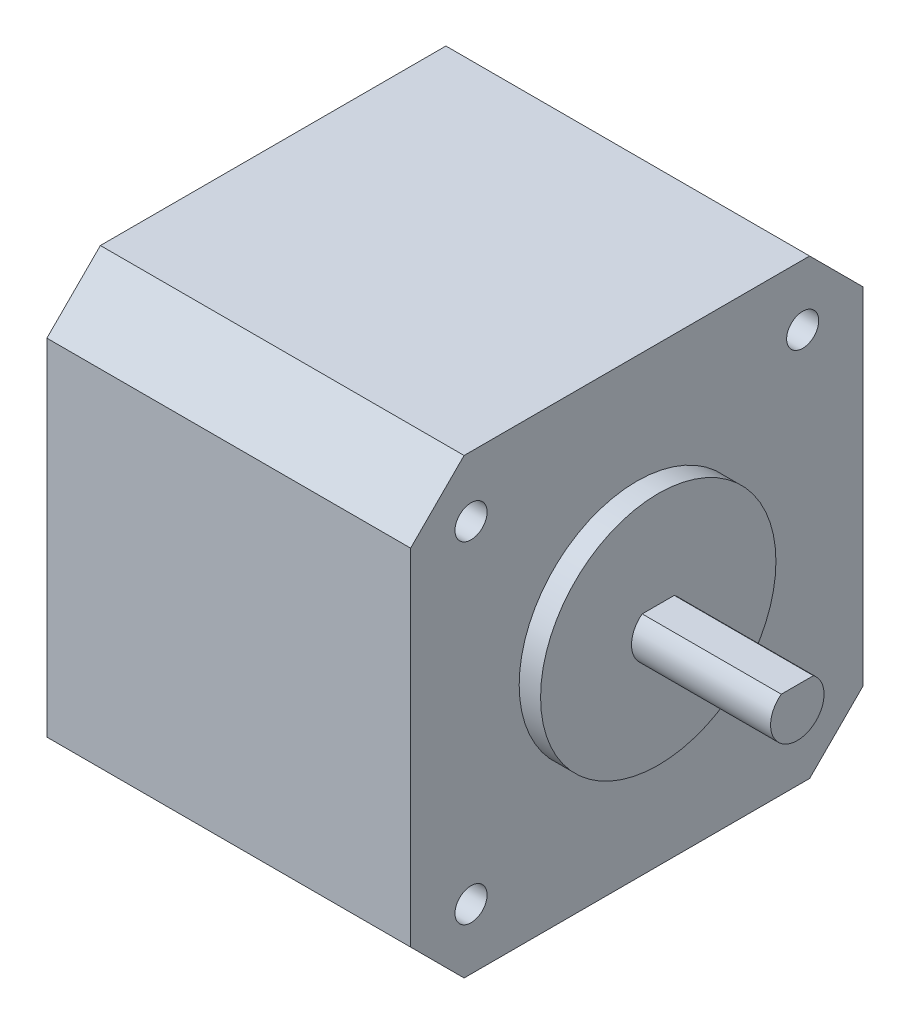
SolidWorks part; units mm, degrees
ref_plane "Front Plane" through (0, 0, 0) normal (0, 0, 1) x (1, 0, 0)
ref_plane "Top Plane" through (0, 0, 0) normal (0, 1, 0) x (1, 0, 0)
ref_plane "Right Plane" through (0, 0, 0) normal (1, 0, 0) x (0, 0, -1)
sketch "Sketch1" plane through (0, 0, 0) normal (1, 0, 0) x (0, 0, -1)
  line L0 (0, 37.3) -> (5, 42.3)
  line L1 (5, 0) -> (37.3, 0)
  line L2 (0, 5) -> (0, 37.3)
  line L3 (5, 42.3) -> (37.3, 42.3)
  line L4 (42.3, 5) -> (42.3, 37.3)
  line L5 (0, 0) -> (42.3, 42.3) construction
  line L6 (0, 42.3) -> (42.3, 0) construction
  line L7 (0, 5) -> (5, 0)
  line L8 (37.3, 0) -> (42.3, 5)
  line L9 (42.3, 37.3) -> (37.3, 42.3)
  circle A0 centre (5.65, 36.65) radius 1.5
  circle A1 centre (36.65, 36.65) radius 1.5
  circle A2 centre (36.65, 5.65) radius 1.5
  circle A3 centre (5.65, 5.65) radius 1.5
  point P4 (21.15, 21.15)
  dimension "D4" = 3
  dimension "D1" = 42.3
  dimension "D2" = 42.3
  dimension "D3" = 31
extrude "Boss-Extrude1" add sketch "Sketch1" along normal blind 34 contours L1 L4 L3 L2 A3 A2 A1 A0
sketch "Sketch2" plane through (34, 0, 0) normal (1, 0, 0) x (0, 0, -1)
  line L0 (0, 21.15) -> (42.3, 21.15) construction
  line L1 (0, 5) -> (0, 37.3) construction
  line L2 (42.3, 5) -> (42.3, 37.3) construction
  line L3 (21.15, 42.3) -> (21.15, 0) construction
  line L4 (5, 42.3) -> (37.3, 42.3) construction
  line L5 (5, 0) -> (37.3, 0) construction
  circle A0 centre (21.15, 21.15) radius 11
  point P12 (21.15, 42.3)
  dimension "D1" = 22
extrude "Boss-Extrude2" add sketch "Sketch2" along normal blind 2 contours A0
sketch "Sketch3" plane through (36, 0, 0) normal (1, 0, 0) x (0, 0, -1)
  line L0 (19.65, 23.15) -> (22.65, 23.15)
  arc A0 (19.65, 23.15) -> (22.65, 23.15) centre (21.15, 21.15) ccw
  circle A1 centre (21.15, 21.15) radius 11
  circle A2 centre (21.15, 21.15) radius 11 construction
  point P6 (21.15, 18.65)
  dimension "D2" = 5
  dimension "D3" = 4.5
  dimension "D1" = 0
extrude "Boss-Extrude3" add sketch "Sketch3" along normal blind 13 contours A0 L0
